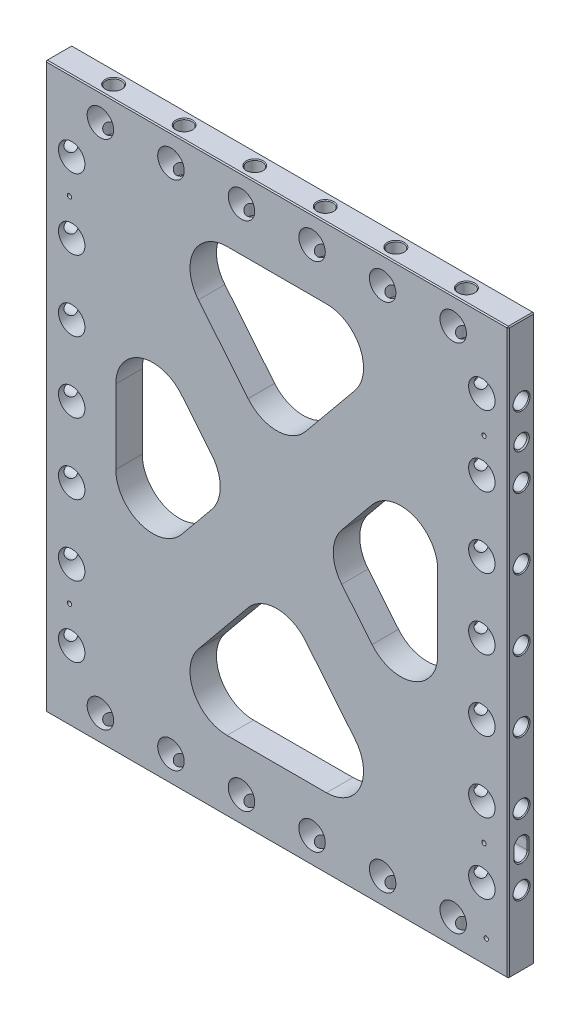
SolidWorks part; units mm, degrees
material "6061-T6 Al"
ref_plane "Front Plane" through (0, 0, 0) normal (0, 0, 1) x (1, 0, 0)
ref_plane "Top Plane" through (0, 0, 0) normal (0, 1, 0) x (1, 0, 0)
ref_plane "Right Plane" through (0, 0, 0) normal (1, 0, 0) x (0, 0, -1)
sketch "Sketch2" plane through (0, 0, 0) normal (0, 0, 1) x (1, 0, 0)
  line L0 (-166.6875, -203.2) -> (166.6875, 203.2) construction
  line L1 (-166.6875, 203.2) -> (166.6875, 203.2)
  line L2 (-166.6875, 203.2) -> (-166.6875, -203.2)
  line L3 (-166.6875, -203.2) -> (166.6875, -203.2)
  line L4 (166.6875, 203.2) -> (166.6875, -203.2)
  point P4 (0, 0)
  dimension "D1" = 333.375
  dimension "D2" = 406.4
extrude "Extrude1" add sketch "Sketch2" along normal mid plane 19.05
sketch "Sketch8" plane through (0, 0, 9.525) normal (0, 0, 1) x (1, 0, 0)
  line L0 (-166.6875, 203.2) -> (166.6875, -203.2) construction
  line L1 (166.6875, 203.2) -> (-166.6875, -203.2) construction
  line L2 (-115.8875, 101.2234) -> (-32.8526, 0)
  line L3 (-32.8526, 0) -> (-115.8875, -101.2234)
  line L4 (-115.8875, -101.2234) -> (-115.8875, 101.2234)
  line L5 (-92.163, 152.4) -> (0, 40.0489)
  line L6 (0, 40.0489) -> (92.163, 152.4)
  line L7 (92.163, 152.4) -> (-92.163, 152.4)
  line L8 (115.8875, 101.2234) -> (115.8875, -101.2234)
  line L9 (115.8875, -101.2234) -> (32.8526, 0)
  line L10 (32.8526, 0) -> (115.8875, 101.2234)
  line L11 (0, -40.0489) -> (-92.163, -152.4)
  line L12 (-92.163, -152.4) -> (92.163, -152.4)
  line L13 (92.163, -152.4) -> (0, -40.0489)
  line L14 (0, -40.0489) -> (-32.8526, 0) construction
  line L15 (-32.8526, 0) -> (0, 40.0489) construction
  line L16 (0, 40.0489) -> (0, 0) construction
  line L17 (0, 0) -> (0, -40.0489) construction
  line L18 (32.8526, 0) -> (0, 0) construction
  line L19 (0, 0) -> (-32.8526, 0) construction
  line L20 (-166.6875, 203.2) -> (-166.6875, -203.2) construction
  line L21 (166.6875, 203.2) -> (-166.6875, 203.2) construction
  point P19 (-16.4263, 20.0245)
  point P23 (-16.4263, -20.0245)
  point P24 (-166.6875, 0)
  dimension "D1" = 50.8
  dimension "D2" = 50.8
  dimension "D3" = 50.8
extrude "Triangles -- Cut-Extrude2" cut sketch "Sketch8" against normal through all
fillet "Triangles -- Fillet1" radius 26.67 12 edges at (-115.8875, -101.2234, 0) (-32.8526, 0, 0) (-92.163, -152.4, 0) (92.163, -152.4, 0) (0, -40.0489, 0) (32.8526, 0, 0) (115.8875, -101.2234, 0) (115.8875, 101.2234, 0) (92.163, 152.4, 0) (-92.163, 152.4, 0) (0, 40.0489, 0) (-115.8875, 101.2234, 0)
hole_wizard "3/4 (0.75) Diameter Hole1" positions "Sketch4" profile "Sketch3" hole size "3/4" standard "Ansi Inch" end condition through all
sketch "Sketch4" plane through (0, 0, 9.525) normal (0, 0, 1) x (1, 0, 0)
  line L3 (0, 0) -> (-147.6375, 0) construction
  line L6 (-166.6875, 203.2) -> (-166.6875, -203.2) construction
  point P0 (-147.6375, 0)
  dimension "D1" = 19.05
sketch "Sketch3" plane through (-147.6375, 0, 9.525) normal (1, 0, 0) x (0, -1, 0)
  line L0 (0, 0) -> (0, 19.05)
  line L1 (0, 19.05) -> (9.525, 19.05)
  line L2 (9.525, 19.05) -> (9.525, 0)
  line L5 (9.525, 0) -> (0, 0)
  line L11 (0, -6.35) -> (0, 107.95) construction
  dimension "Thru Hole Dia." = 19.05
  dimension "Thru Hole Depth" = 19.05
hole_wizard "7/16 (0.4375) Diameter Hole1" positions "Sketch6" profile "Sketch5" hole size "7/16" standard "Ansi Inch"
sketch "Sketch6" plane through (-166.6875, 0, 0) normal (-1, 0, 0) x (0, 0, 1)
  point P0 (0, 0)
sketch "Sketch5" plane through (-166.6875, 0, 0) normal (0, 1, 0) x (0, 0, 1)
  line L0 (0, 0) -> (0, 38.2635)
  line L1 (0, 38.2635) -> (5.5562, 34.925)
  line L2 (5.5562, 34.925) -> (5.5562, 0.6209)
  line L3 (5.5562, 0.6209) -> (6.096, 0)
  line L5 (6.096, 0) -> (0, 0)
  line L6 (-5.5562, 0.6209) -> (-6.096, 0) construction
  line L10 (0, 38.2635) -> (-5.5563, 34.925) construction
  line L11 (0, -6.35) -> (0, 107.95) construction
  dimension "Hole Dia." = 11.1125
  dimension "Hole Depth" = 34.925
  dimension "Near C'Sink Dia." = 12.192
  dimension "Near C'Sink Angle" = 82
  dimension "Drill Angle" = 118
pattern_linear "LPattern3" count 4 spacing 50.8 along (0, 1, 0) count 4 spacing 50.8 along (0, -1, 0) of "7/16 (0.4375) Diameter Hole1", "3/4 (0.75) Diameter Hole1"
mirror "Mirror1" about plane through (0, 0, 0) normal (1, 0, 0) of "3/4 (0.75) Diameter Hole1", "7/16 (0.4375) Diameter Hole1", "LPattern3"
hole_wizard "3/4 (0.75) Diameter Hole2" positions "Sketch11" profile "Sketch10" hole size "3/4" standard "Ansi Inch" end condition through all
sketch "Sketch11" plane through (0, 0, 9.525) normal (0, 0, 1) x (1, 0, 0)
  line L2 (-166.6875, -203.2) -> (166.6875, -203.2) construction
  line L3 (25.4, -184.15) -> (-25.4, -184.15) construction
  line L7 (0, -184.15) -> (0, 0) construction
  line L10 (25.4, -184.15) -> (76.2, -184.15) construction
  line L13 (-25.4, -184.15) -> (-76.2, -184.15) construction
  line L14 (76.2, -184.15) -> (127, -184.15) construction
  line L15 (127, -184.15) -> (177.8, -184.15) construction
  line L18 (-76.2, -184.15) -> (-127, -184.15) construction
  line L19 (-127, -184.15) -> (-177.8, -184.15) construction
  point P0 (-25.4, -184.15)
  point P11 (25.4, -184.15)
  point P13 (76.2, -184.15)
  point P15 (-76.2, -184.15)
  point P40 (-127, -184.15)
  point P44 (127, -184.15)
  dimension "D1" = 19.05
  dimension "D2" = 50.8
sketch "Sketch10" plane through (-25.4, -184.15, 9.525) normal (1, 0, 0) x (0, -1, 0)
  line L0 (0, 0) -> (0, 19.05)
  line L1 (0, 19.05) -> (9.525, 19.05)
  line L2 (9.525, 19.05) -> (9.525, 0)
  line L5 (9.525, 0) -> (0, 0)
  line L11 (0, -6.35) -> (0, 107.95) construction
  dimension "Thru Hole Dia." = 19.05
  dimension "Thru Hole Depth" = 19.05
hole_wizard "7/16 (0.4375) Diameter Hole2" positions "Sketch13" profile "Sketch12" hole size "7/16" standard "Ansi Inch"
sketch "Sketch13" plane through (0, -203.2, 0) normal (0, -1, 0) x (1, 0, 0)
  line L0 (85.725, 9.525) -> (66.675, 9.525) construction
  line L1 (34.925, 9.525) -> (15.875, 9.525) construction
  line L2 (-15.875, 9.525) -> (-34.925, 9.525) construction
  line L3 (-66.675, 9.525) -> (-85.725, 9.525) construction
  line L4 (85.725, 9.525) -> (66.675, 9.525) construction
  line L5 (34.925, 9.525) -> (15.875, 9.525) construction
  line L6 (-15.875, 9.525) -> (-34.925, 9.525) construction
  line L7 (-66.675, 9.525) -> (-85.725, 9.525) construction
  line L8 (-76.2, 9.525) -> (-76.2, -9.525) construction
  line L9 (-166.6875, -9.525) -> (166.6875, -9.525) construction
  line L12 (-25.4, 9.525) -> (-25.4, -9.525) construction
  line L15 (25.4, 9.525) -> (25.4, -9.525) construction
  line L18 (76.2, 9.525) -> (76.2, -9.525) construction
  line L20 (136.525, 9.525) -> (117.475, 9.525) construction
  line L22 (-117.475, 9.525) -> (-136.525, 9.525) construction
  line L24 (136.525, 9.525) -> (117.475, 9.525)
  line L26 (-117.475, 9.525) -> (-136.525, 9.525)
  line L30 (-127, 9.525) -> (-127, -9.525) construction
  line L33 (127, 9.525) -> (127, -9.525) construction
  point P0 (-25.4, 0)
  point P4 (-76.2, 0)
  point P6 (25.4, 0)
  point P8 (76.2, 0)
  point P39 (-127, 0)
  point P43 (127, 0)
sketch "Sketch12" plane through (-25.4, -203.2, 0) normal (1, 0, 0) x (0, 0, -1)
  line L0 (0, 0) -> (0, 38.2635)
  line L1 (0, 38.2635) -> (5.5562, 34.925)
  line L2 (5.5562, 34.925) -> (5.5562, 0.6209)
  line L3 (5.5562, 0.6209) -> (6.096, 0)
  line L5 (6.096, 0) -> (0, 0)
  line L6 (-5.5562, 0.6209) -> (-6.096, 0) construction
  line L10 (0, 38.2635) -> (-5.5563, 34.925) construction
  line L11 (0, -6.35) -> (0, 107.95) construction
  dimension "Hole Dia." = 11.1125
  dimension "Hole Depth" = 34.925
  dimension "Near C'Sink Dia." = 12.192
  dimension "Near C'Sink Angle" = 82
  dimension "Drill Angle" = 118
mirror "Mirror2" about plane through (0, 0, 0) normal (0, 1, 0) of "3/4 (0.75) Diameter Hole2", "7/16 (0.4375) Diameter Hole2"
hole_wizard "3/8 (0.375) Pin Hole1" positions "Sketch15" profile "Sketch14" counterbore size "3/8" standard "Ansi Inch"
sketch "Sketch15" plane through (0, -203.2, 0) normal (0, -1, 0) x (1, 0, 0)
  line L0 (150.8125, 0) -> (166.6875, 0) construction
  line L1 (166.6875, 9.525) -> (166.6875, -9.525) construction
  point P0 (150.8125, 0)
  dimension "D1" = 15.875
sketch "Sketch14" plane through (150.8125, -203.2, 0) normal (1, 0, 0) x (0, 0, -1)
  line L0 (0, 0) -> (0, 21.9116)
  line L1 (0, 21.9116) -> (4.7625, 19.05)
  line L2 (4.7625, 19.05) -> (4.7625, 3.175)
  line L3 (4.7625, 3.175) -> (4.7879, 3.175)
  line L5 (4.7879, 3.175) -> (4.7879, 0.6282)
  line L6 (4.7879, 0.6282) -> (5.334, 0)
  line L7 (5.334, 0) -> (0, 0)
  line L8 (-4.7879, 0.6282) -> (-5.334, 0) construction
  line L10 (0, 21.9116) -> (-4.7625, 19.05) construction
  line L11 (0, -6.35) -> (0, 107.95) construction
  dimension "Hole Dia." = 9.525
  dimension "Hole Depth" = 19.05
  dimension "C'Bore Dia." = 9.5758
  dimension "C'Bore Depth" = 3.175
  dimension "Near C'Sink Dia." = 10.668
  dimension "Near C'Sink Angle" = 82
  dimension "Drill Angle" = 118
hole_wizard "3/8 (0.376) Pin Locate1" positions "Sketch17" profile "Sketch16" hole size "3/8" standard "Ansi Inch"
sketch "Sketch17" plane through (-166.6875, 0, 0) normal (-1, 0, 0) x (0, 0, 1)
  line L1 (0, 101.6) -> (0, 152.4) construction
  point P0 (0, 127)
sketch "Sketch16" plane through (-166.6875, 127, 0) normal (0, 1, 0) x (0, 0, 1)
  line L0 (0, 0) -> (0, 21.9192)
  line L1 (0, 21.9192) -> (4.7752, 19.05)
  line L2 (4.7752, 19.05) -> (4.7752, 0.935)
  line L3 (4.7752, 0.935) -> (5.588, 0)
  line L5 (5.588, 0) -> (0, 0)
  line L6 (-4.7752, 0.935) -> (-5.588, 0) construction
  line L10 (0, 21.9192) -> (-4.7752, 19.05) construction
  line L11 (0, -6.35) -> (0, 107.95) construction
  dimension "Hole Dia." = 9.5504
  dimension "Hole Depth" = 19.05
  dimension "Near C'Sink Dia." = 11.176
  dimension "Near C'Sink Angle" = 82
  dimension "Drill Angle" = 118
hole_wizard "3/8 (0.376) Pin Locate2" positions "Sketch19" profile "Sketch18" hole size "3/8" standard "Ansi Inch"
sketch "Sketch19" plane through (166.6875, 0, 0) normal (1, 0, 0) x (0, 0, -1)
  line L0 (0, 101.6) -> (0, 152.4) construction
  point P0 (0, 127)
sketch "Sketch18" plane through (166.6875, 127, 0) normal (0, 1, 0) x (0, 0, -1)
  line L0 (0, 0) -> (0, 21.9192)
  line L1 (0, 21.9192) -> (4.7752, 19.05)
  line L2 (4.7752, 19.05) -> (4.7752, 0.935)
  line L3 (4.7752, 0.935) -> (5.588, 0)
  line L5 (5.588, 0) -> (0, 0)
  line L6 (-4.7752, 0.935) -> (-5.588, 0) construction
  line L10 (0, 21.9192) -> (-4.7752, 19.05) construction
  line L11 (0, -6.35) -> (0, 107.95) construction
  dimension "Hole Dia." = 9.5504
  dimension "Hole Depth" = 19.05
  dimension "Near C'Sink Dia." = 11.176
  dimension "Near C'Sink Angle" = 82
  dimension "Drill Angle" = 118
sketch "Sketch20" plane through (-166.6875, 0, 0) normal (-1, 0, 0) x (0, 0, 1)
  line L0 (0, -152.4) -> (0, -127) construction
  line L1 (0, -127) -> (0, -101.6) construction
  line L2 (0, -130.175) -> (0, -123.825) construction
  line L3 (4.7752, -130.175) -> (4.7752, -123.825)
  line L4 (-4.7752, -130.175) -> (-4.7752, -123.825)
  arc A0 (4.7752, -130.175) -> (-4.7752, -130.175) centre (0, -130.175) cw
  arc A1 (4.7752, -123.825) -> (-4.7752, -123.825) centre (0, -123.825) ccw
  point P8 (0, -127)
  dimension "D1" = 6.35
  dimension "D2" = 9.5504
  dimension "D3" = 4.7752
extrude "Slot Locate1" cut sketch "Sketch20" against normal blind 19.05
chamfer "Chamfer1" distance 0.762 angle 45 4 edges at (-166.6875, -127, 4.7752) (-166.6875, -119.0498, 0) (-166.6875, -134.9502, 0) (-166.6875, -127, -4.7752)
sketch "Sketch21" plane through (166.6875, 0, 0) normal (1, 0, 0) x (0, 0, -1)
  line L0 (0, -152.4) -> (0, -127) construction
  line L1 (0, -127) -> (0, -101.6) construction
  line L2 (0, -123.825) -> (0, -130.175) construction
  line L3 (-4.7752, -123.825) -> (-4.7752, -130.175)
  line L4 (4.7752, -123.825) -> (4.7752, -130.175)
  arc A0 (-4.7752, -123.825) -> (4.7752, -123.825) centre (0, -123.825) cw
  arc A1 (-4.7752, -130.175) -> (4.7752, -130.175) centre (0, -130.175) ccw
  point P8 (0, -127)
  dimension "D1" = 6.35
  dimension "D2" = 9.5504
  dimension "D3" = 4.7752
extrude "Slot Locate2" cut sketch "Sketch21" against normal blind 19.05
chamfer "Chamfer2" distance 0.762 angle 45 4 edges at (166.6875, -127, -4.7752) (166.6875, -119.0498, 0) (166.6875, -134.9502, 0) (166.6875, -127, 4.7752)
hole_wizard "1/8 (0.125) Diameter Hole1" positions "Sketch23" profile "Sketch24" hole size "1/8" standard "Ansi Inch"
sketch "Sketch23" plane through (0, 0, 9.525) normal (0, 0, 1) x (1, 0, 0)
  line L0 (-147.6375, -130.175) -> (-147.6375, -123.825) construction
  line L1 (-147.6375, 131.7752) -> (-147.6375, 122.2248) construction
  line L2 (147.6375, 131.7752) -> (147.6375, 122.2248) construction
  line L3 (147.6375, -123.825) -> (147.6375, -130.175) construction
  line L5 (-147.6375, -130.175) -> (-147.6375, -123.825)
  line L6 (-147.6375, 131.7752) -> (-147.6375, 122.2248)
  line L7 (147.6375, 131.7752) -> (147.6375, 122.2248)
  line L8 (147.6375, -123.825) -> (147.6375, -130.175)
  line L10 (150.8125, -184.15) -> (150.8125, -185.7375) construction
  line L13 (147.6375, -127) -> (149.225, -127) construction
  line L16 (147.6375, 127) -> (149.225, 127) construction
  line L19 (-147.6375, -127) -> (-149.225, -127) construction
  line L22 (-147.6375, 127) -> (-149.225, 127) construction
  line L23 (155.575, -184.15) -> (146.05, -184.15) construction
  line L24 (155.575, -184.15) -> (146.05, -184.15)
  point P0 (150.8125, -185.7375)
  point P40 (149.225, -127)
  point P42 (149.225, 127)
  point P44 (-149.225, 127)
  point P46 (-149.225, -127)
  dimension "D1" = 1.5875
sketch "Sketch24" plane through (150.8125, -185.7375, 9.525) normal (1, 0, 0) x (0, -1, 0)
  line L0 (0, 0) -> (0, 10.4789)
  line L1 (0, 10.4789) -> (1.5875, 9.525)
  line L2 (1.5875, 9.525) -> (1.5875, 0)
  line L5 (1.5875, 0) -> (0, 0)
  line L10 (0, 10.4789) -> (-1.5875, 9.525) construction
  line L11 (0, -6.35) -> (0, 107.95) construction
  dimension "Hole Dia." = 3.175
  dimension "Hole Depth" = 9.525
  dimension "Drill Angle" = 118
chamfer "Chamfer3" distance 0.762 angle 45 12 edges at (0, -203.2, -9.525) (0, -203.2, 9.525) (166.6875, -203.2, 0) (-166.6875, -203.2, 0) (-166.6875, 0, -9.525) (-166.6875, 0, 9.525) (166.6875, 0, -9.525) (166.6875, 0, 9.525) (166.6875, 203.2, 0) (0, 203.2, -9.525) (-166.6875, 203.2, 0) (0, 203.2, 9.525)
